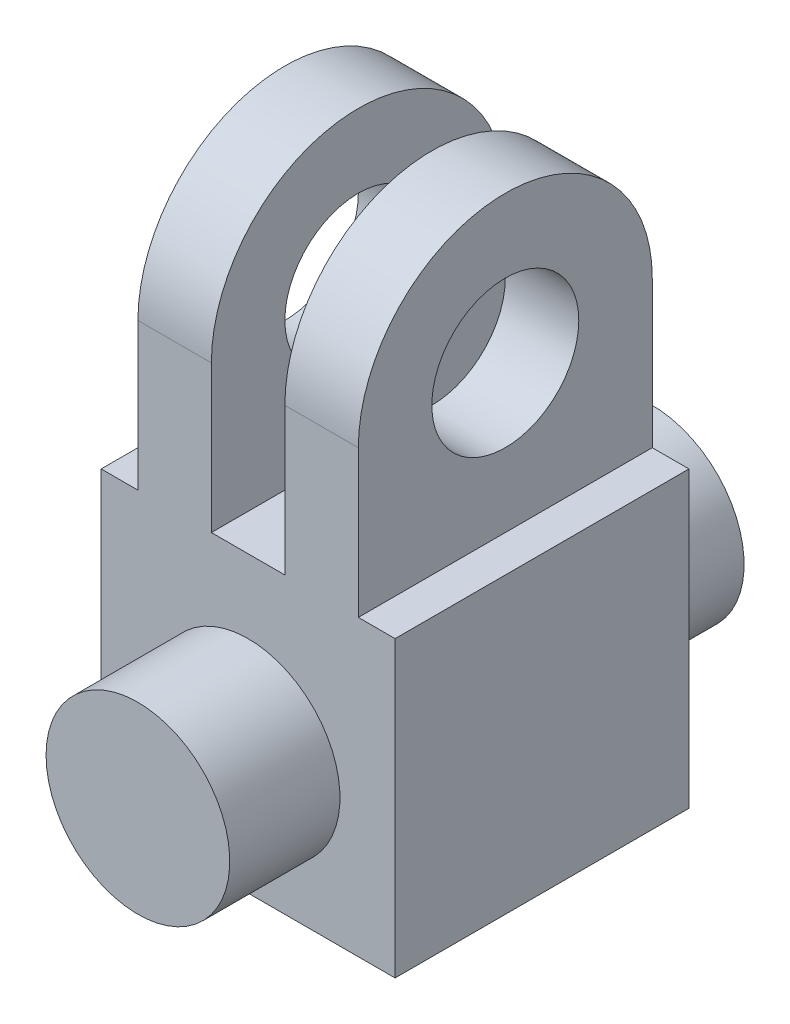
SolidWorks part; units mm, degrees
ref_plane "Alzado" through (0, 0, 0) normal (0, 0, 1) x (1, 0, 0)
ref_plane "Planta" through (0, 0, 0) normal (0, 1, 0) x (1, 0, 0)
ref_plane "Vista lateral" through (0, 0, 0) normal (1, 0, 0) x (0, 0, -1)
sketch "Croquis1" plane through (0, 0, 0) normal (0, 1, 0) x (1, 0, 0)
  line L1 (0, 0) -> (80, 0)
  line L2 (0, 0) -> (0, -80)
  line L3 (0, -80) -> (80, -80)
  line L4 (80, 0) -> (80, -80)
  dimension "D1" = 80
  dimension "D2" = 80
extrude "Saliente-Extruir1" add sketch "Croquis1" along normal blind 160
sketch "Croquis2" plane through (0, 160, 0) normal (0, 1, 0) x (1, 0, 0)
  line L0 (0, -80) -> (80, -80) construction
  line L1 (0, 0) -> (10, 0)
  line L2 (0, 0) -> (0, -80)
  line L3 (0, -80) -> (10, -80)
  line L4 (10, 0) -> (10, -80)
  line L6 (80, 0) -> (70, 0)
  line L7 (80, 0) -> (80, -80)
  line L8 (80, -80) -> (70, -80)
  line L9 (70, 0) -> (70, -80)
  dimension "D1" = 10
  dimension "D2" = 10
extrude "Cortar-Extruir1" cut sketch "Croquis2" against normal blind 80
sketch "Croquis3" plane through (0, 160, 0) normal (0, 1, 0) x (1, 0, 0)
  line L0 (70, 0) -> (10, 0) construction
  line L1 (30, 0) -> (50, 0)
  line L2 (30, 0) -> (30, -80)
  line L3 (30, -80) -> (50, -80)
  line L4 (50, 0) -> (50, -80)
  line L5 (10, -80) -> (70, -80) construction
  dimension "D1" = 20
  dimension "D2" = 20
extrude "Cortar-Extruir2" cut sketch "Croquis3" against normal blind 80
sketch "Croquis4" plane through (70, 0, 0) normal (1, 0, 0) x (0, 0, -1)
  line L0 (-40, 80) -> (-40, 120) construction
  line L1 (-80, 80) -> (0, 80) construction
  line L2 (-80, 120) -> (-80, 160)
  line L3 (-40, 160) -> (0, 160)
  line L4 (0, 160) -> (0, 120)
  circle A0 centre (-40, 120) radius 20
  circle A1 centre (-40, 120) radius 40
  dimension "D2" = 40
  dimension "D1" = 40
extrude "Cortar-Extruir3" cut sketch "Croquis4" against normal blind 80
sketch "Croquis5" plane through (0, 0, 0) normal (0, 0, -1) x (-1, 0, 0)
  line L0 (-40, 0) -> (-40, 35) construction
  line L1 (-80, 0) -> (0, 0) construction
  circle A0 centre (-40, 35) radius 25
  dimension "D1" = 50
extrude "Saliente-Extruir2" add sketch "Croquis5" along normal blind 30 and the other way blind 110
